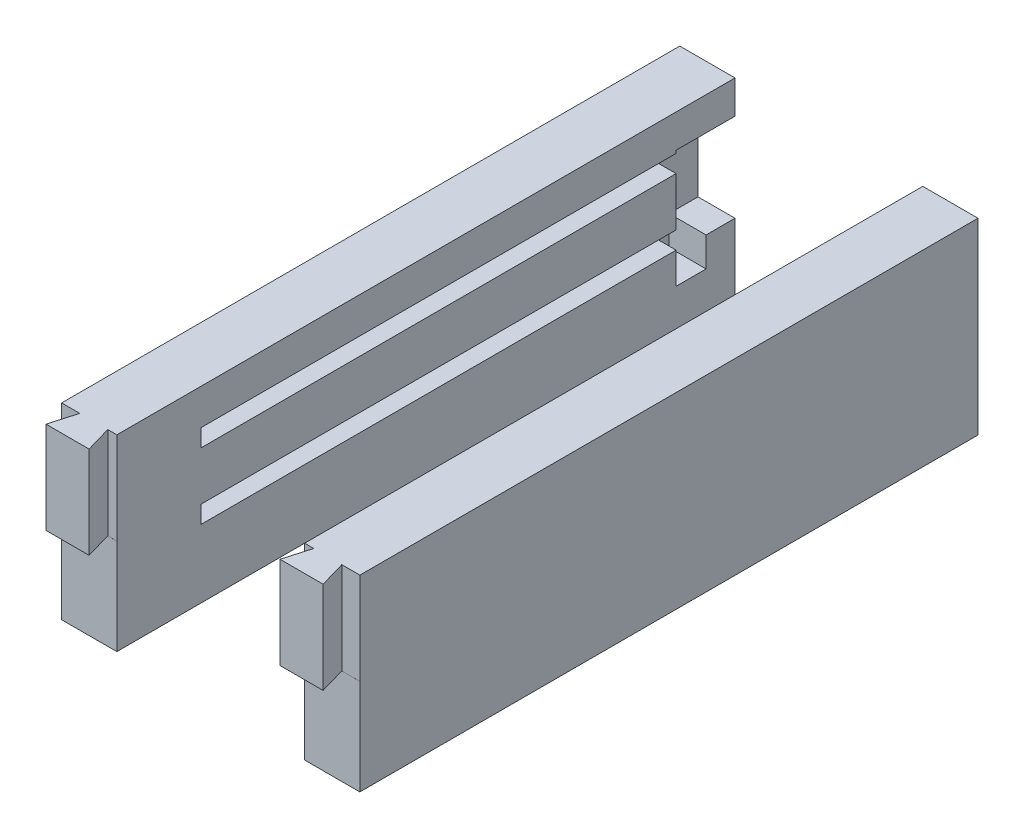
SolidWorks part; units mm, degrees
ref_plane "Front Plane" through (0, 0, 0) normal (0, 0, 1) x (1, 0, 0)
ref_plane "Top Plane" through (0, 0, 0) normal (0, 1, 0) x (1, 0, 0)
ref_plane "Right Plane" through (0, 0, 0) normal (1, 0, 0) x (0, 0, -1)
sketch "Sketch1" plane through (0, 0, 0) normal (1, 0, 0) x (0, 0, -1)
  line L1 (-64.5621, 30.5573) -> (110.4379, 30.5573)
  line L2 (-64.5621, 30.5573) -> (-64.5621, -20.4427)
  line L3 (-64.5621, -20.4427) -> (110.4379, -20.4427)
  line L4 (110.4379, 30.5573) -> (110.4379, -20.4427)
  dimension "D1" = 175
  dimension "D2" = 51
extrude "Boss-Extrude1" add sketch "Sketch1" along normal blind 15 contours L2 L3 L4 L1
sketch "Sketch7" plane through (0, 0, -110.4379) normal (0, 0, -1) x (-1, 0, 0)
  line L0 (-15, -20.4427) -> (-15, -1.9427)
  line L1 (-15, 2.8073) -> (-15, 16.0573)
  line L2 (-10.25, 2.8073) -> (-15, 2.8073)
  line L3 (-10.25, 2.8073) -> (-10.25, -1.9427)
  line L4 (-10.25, -1.9427) -> (-15, -1.9427)
  line L5 (-15, 2.8073) -> (-15, -1.9427)
  line L6 (-15, 30.5573) -> (-15, -20.4427) construction
  line L8 (-15, 16.0573) -> (-10.25, 16.0573)
  line L9 (-15, 16.0573) -> (-15, 20.8073)
  line L10 (-15, 20.8073) -> (-10.25, 20.8073)
  line L11 (-10.25, 16.0573) -> (-10.25, 20.8073)
  line M6 (-15, 30.5573) -> (-15, -20.4427)
  dimension "D1" = 18.5
  dimension "D2" = 4.75
  dimension "D3" = 4.75
  dimension "D4" = 13.25
  dimension "D5" = 4.75
  dimension "D6" = 4.75
extrude "Cut-Extrude5" cut sketch "Sketch7" against normal blind 145 contours L4 L3 L2 M6 | L9 L8 L11 L10
sketch "Sketch10" plane through (0, 0, -110.4379) normal (0, 0, -1) x (-1, 0, 0)
  line L0 (-15, -20.4427) -> (-15, -2.4427)
  line L3 (-15, -2.4427) -> (-4.95, -2.4427)
  line L4 (-15, -2.4427) -> (-15, 21.5573)
  line L5 (-15, 21.5573) -> (-4.95, 21.5573)
  line L6 (-4.95, -2.4427) -> (-4.95, 21.5573)
  line M4 (-10.25, 2.8073) -> (-10.25, -1.9427)
  line M5 (-10.25, -1.9427) -> (-15, -1.9427)
  line M6 (-15, -1.9427) -> (-15, -20.4427)
  line M10 (-15, 30.5573) -> (-15, 20.8073)
  line M11 (-15, 2.8073) -> (-10.25, 2.8073)
  dimension "D1" = 18
  dimension "D2" = 24
  dimension "D3" = 10.05
extrude "Cut-Extrude6" cut sketch "Sketch10" against normal blind 16 contours L3 L6 L5 M10 M11 M4 M5 M6
sketch "Sketch11" plane through (0, -2.4427, 0) normal (0, 1, 0) x (1, 0, 0)
  line L0 (4.95, 94.4379) -> (4.95, 110.4379) construction
  line L1 (15, 94.4379) -> (4.95, 94.4379)
  line L2 (15, 94.4379) -> (15, 102.5879)
  line L3 (15, 102.5879) -> (4.95, 102.5879)
  line L4 (4.95, 94.4379) -> (4.95, 102.5879)
  dimension "D1" = 8.15
extrude "Cut-Extrude7" cut sketch "Sketch11" against normal blind 8
sketch "Sketch12" plane through (0, 30.5573, 0) normal (0, 1, 0) x (1, 0, 0)
  line L0 (0, -57.4487) -> (4.9097, -57.4487)
  line L1 (0, -64.5621) -> (0, 110.4379) construction
  line L2 (4.9097, -57.4487) -> (2.87, -64.5621)
  line L3 (15, -64.5621) -> (0, -64.5621) construction
  line L4 (2.87, -64.5621) -> (0, -64.5621)
  line L5 (0, -64.5621) -> (0, -57.4487)
  line L6 (15, -57.4487) -> (15, -64.5621)
  line L7 (15, -64.5621) -> (15, 110.4379) construction
  line L8 (15, -64.5621) -> (14.57, -64.5621)
  line L9 (14.57, -64.5621) -> (12.5303, -57.4487)
  line L10 (12.5303, -57.4487) -> (15, -57.4487)
  dimension "D1" = 7.4
  dimension "D2" = 7.4
  dimension "D3" = 106
  dimension "D4" = 106
  dimension "D5" = 11.7
  dimension "D6" = 2.87
extrude "Cut-Extrude8" cut sketch "Sketch12" against normal blind 25
sketch "Sketch13" plane through (0, -20.4427, 0) normal (0, -1, 0) x (1, 0, 0)
  line L0 (15, 64.5621) -> (15, -110.4379) construction
  line L1 (0, 64.5621) -> (15, 64.5621)
  line L2 (0, 64.5621) -> (0, 57.4521)
  line L3 (0, 57.4521) -> (15, 57.4521)
  line L4 (15, 64.5621) -> (15, 57.4521)
  dimension "D1" = 7.11
extrude "Cut-Extrude9" cut sketch "Sketch13" against normal blind 26
ref_plane "Plane1" through (40.5, 0, 0) normal (1, 0, 0) x (0, 0, -1)
mirror "Mirror4" about plane through (40.5, 0, 0) normal (1, 0, 0) of bodies 116 113
